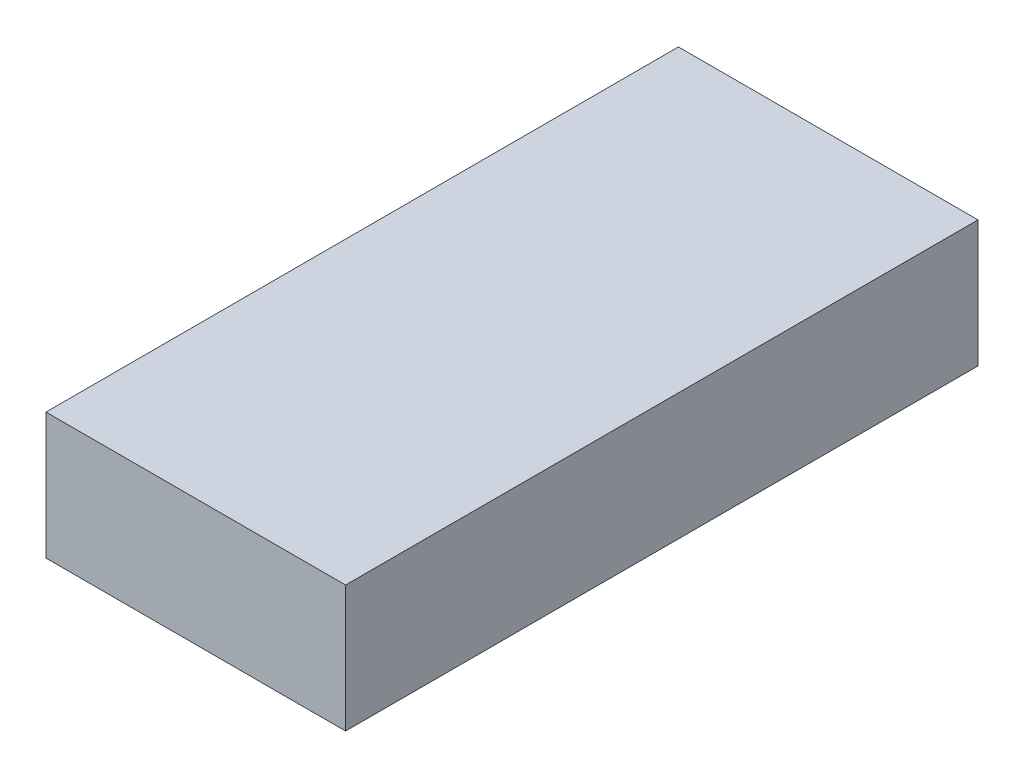
SolidWorks part; units mm, degrees
ref_plane "Front Plane" through (0, 0, 0) normal (0, 0, 1) x (1, 0, 0)
ref_plane "Top Plane" through (0, 0, 0) normal (0, 1, 0) x (1, 0, 0)
ref_plane "Right Plane" through (0, 0, 0) normal (1, 0, 0) x (0, 0, -1)
sketch "Sketch1" plane through (0, 0, 0) normal (0, 1, 0) x (1, 0, 0)
  line L1 (-699.6226, 483.9623) -> (200.3774, 483.9623)
  line L2 (-699.6226, 483.9623) -> (-699.6226, -1416.0377)
  line L3 (-699.6226, -1416.0377) -> (200.3774, -1416.0377)
  line L4 (200.3774, 483.9623) -> (200.3774, -1416.0377)
  dimension "D1" = 1900
  dimension "D2" = 900
extrude "Boss-Extrude1" add sketch "Sketch1" along normal blind 380
